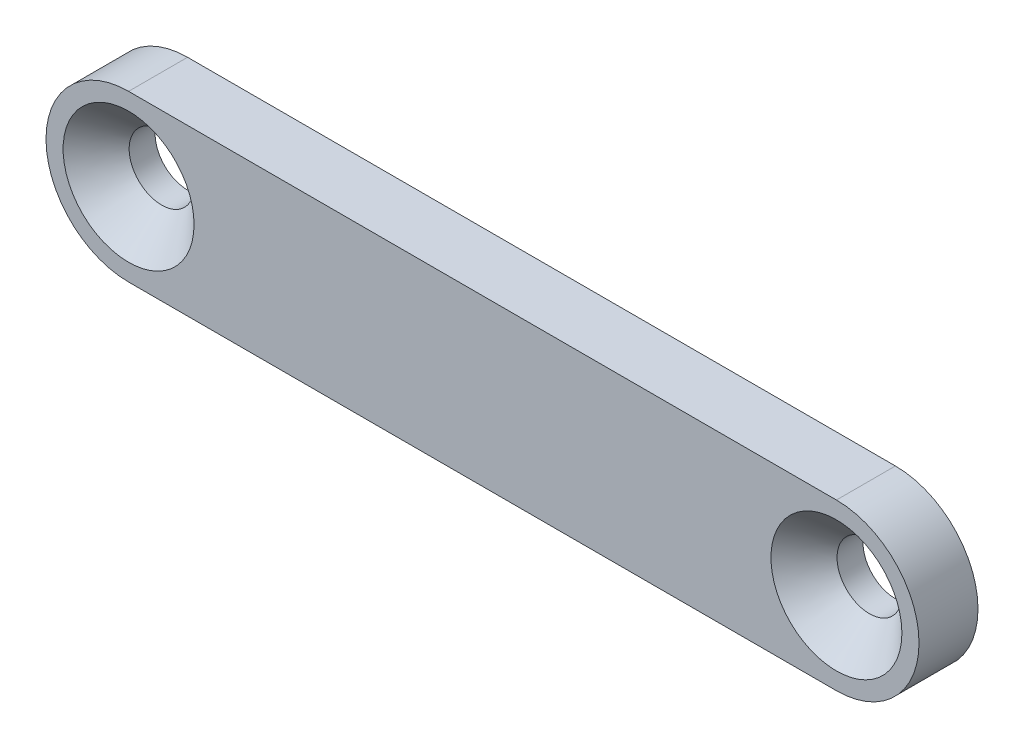
SolidWorks part; units mm, degrees
ref_plane "Plan de face" through (0, 0, 0) normal (0, 0, 1) x (1, 0, 0)
ref_plane "Plan de dessus" through (0, 0, 0) normal (0, 1, 0) x (1, 0, 0)
ref_plane "Plan de droite" through (0, 0, 0) normal (1, 0, 0) x (0, 0, -1)
sketch "Esquisse1" plane through (0, 0, 0) normal (0, 0, 1) x (1, 0, 0)
  line L0 (0, 0) -> (60, 0) construction
  line L1 (0, 7) -> (60, 7)
  line L2 (0, -7) -> (60, -7)
  arc A0 (0, 7) -> (0, -7) centre (0, 0) ccw
  arc A1 (60, -7) -> (60, 7) centre (60, 0) ccw
  circle A2 centre (60, 0) radius 2.75
  circle A3 centre (0, 0) radius 2.75
  point P3 (30, 0)
  dimension "D3" = 5.5
  dimension "D4" = 5.5
  dimension "D1" = 60
  dimension "D2" = 14
extrude "Boss.-Extru.1" add sketch "Esquisse1" along normal blind 5
chamfer "Chanfrein1" distance 2.8 angle 45 2 edges at (62.75, 0, 5) (2.75, 0, 5)
